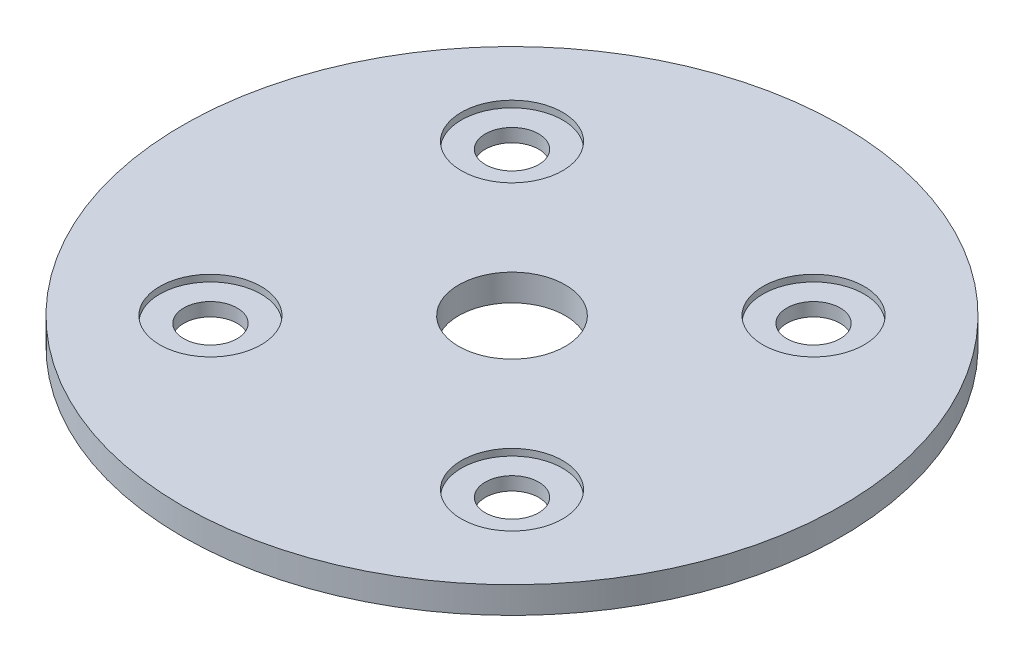
SolidWorks part; units mm, degrees
ref_plane "Front Plane" through (0, 0, 0) normal (0, 0, 1) x (1, 0, 0)
ref_plane "Top Plane" through (0, 0, 0) normal (0, 1, 0) x (1, 0, 0)
ref_plane "Right Plane" through (0, 0, 0) normal (1, 0, 0) x (0, 0, -1)
sketch "Sketch2" plane through (0, 0, 0) normal (0, 1, 0) x (1, 0, 0)
  circle A0 centre (0, 0) radius 39.2557
  dimension "D1" = 78.5114
extrude "Boss-Extrude1" add sketch "Sketch2" along normal mid plane 3.175
sketch "Sketch3" plane through (0, 1.5875, 0) normal (0, 1, 0) x (1, 0, 0)
  line L0 (-1000, 0) -> (49000, 0) construction
  line L1 (-17.9605, -17.9605) -> (17.9605, 17.9605) construction
  line L2 (17.9605, 17.9605) -> (0, 0) construction
  line L3 (-17.9605, 17.9605) -> (17.9605, -17.9605) construction
  point P9 (0, 0)
  point P19 (-17.9605, 17.9605)
  point P22 (17.9605, 17.9605)
  point P25 (17.9605, -17.9605)
  point P28 (-17.9605, -17.9605)
  dimension "D1" = 45
  dimension "D2" = 50.8
hole_wizard "1/4 (0.25) Diameter Hole1" positions "Sketch3" profile "Sketch7" hole size "1/4" standard "ANSI Inch"
sketch "Sketch7" plane through (-17.9605, 1.5875, 17.9605) normal (1, 0, 0) x (0, 0, 1)
  line L0 (0, 0) -> (0, 3.175)
  line L1 (0, 3.175) -> (3.175, 3.175)
  line L2 (3.175, 3.175) -> (3.175, 0)
  line L5 (3.175, 0) -> (0, 0)
  line L11 (0, -6.35) -> (0, 107.95) construction
  dimension "Thru Hole Dia." = 6.35
  dimension "Thru Hole Depth" = 3.175
sketch "Sketch8" plane through (0, 1.5875, 0) normal (0, 1, 0) x (1, 0, 0)
  point P0 (0, 0)
hole_wizard "1/2 (0.5) Diameter Hole1" positions "Sketch8" profile "Sketch9" hole size "1/2" standard "ANSI Inch" end condition through all
sketch "Sketch9" plane through (0, 1.5875, 0) normal (1, 0, 0) x (0, 0, 1)
  line L0 (0, 0) -> (0, 3.175)
  line L1 (0, 3.175) -> (6.35, 3.175)
  line L2 (6.35, 3.175) -> (6.35, 0)
  line L5 (6.35, 0) -> (0, 0)
  line L11 (0, -6.35) -> (0, 107.95) construction
  dimension "Thru Hole Dia." = 12.7
  dimension "Thru Hole Depth" = 3.175
sketch "Sketch10" plane through (0, 1.5875, 0) normal (0, 1, 0) x (1, 0, 0)
  circle A0 centre (-17.9605, 17.9605) radius 6.0325
  circle A1 centre (17.9605, 17.9605) radius 6.0325
  circle A2 centre (17.9605, -17.9605) radius 6.0325
  circle A3 centre (-17.9605, -17.9605) radius 6.0325
  dimension "D1" = 12.065
extrude "Cut-Extrude1" cut sketch "Sketch10" against normal blind 0.7937
mirror "Mirror1" about plane through (0, 0, 0) normal (0, 1, 0) of "Cut-Extrude1"
equation "\"AIRFRAME_OD\"= 3.091in"
equation "\"AIRFRAME_ID\"= 3.00in"
equation "\"FLAT_T\"= 0.125in"
equation "\"NOSE_EXP_L\"= 3.5in"
equation "\"NOSE_SHOULDER_L\"= 5in"
equation "\"MAIN_L\"= 30in"
equation "\"RECO_COUP_L\"= 6in"
equation "\"RECO_SWITCH_L\"= 1.5in"
equation "\"DROGUE_L\"= 14in"
equation "\"ATS_FORE_COUP_L\"= 4in"
equation "\"ATS_AFT_COUP_L\"= 2.5in"
equation "\"LOWER_L\"= 16in"
equation "\"FIN_N\"= 4"
equation "\"CR_AFT_X\"= 0.5in"
equation "\"CR_FORE_X\"= 6in"
equation "\"D1@Sketch2\"=\"AIRFRAME_OD\""
equation "\"D1@Boss-Extrude1\"=\"FLAT_T\""
